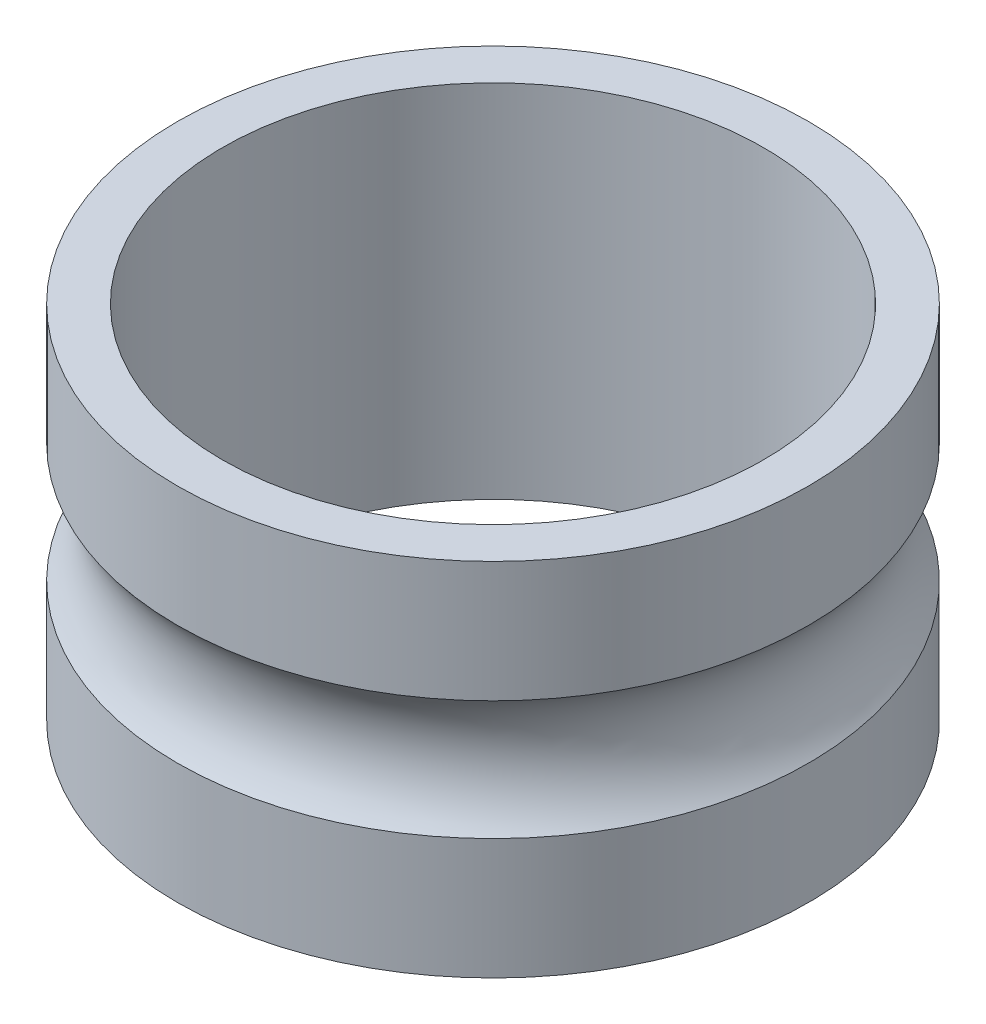
SolidWorks part; units mm, degrees
material "Chrome Stainless Steel"
ref_plane "Front Plane" through (0, 0, 0) normal (0, 0, 1) x (1, 0, 0)
ref_plane "Top Plane" through (0, 0, 0) normal (0, 1, 0) x (1, 0, 0)
ref_plane "Right Plane" through (0, 0, 0) normal (1, 0, 0) x (0, 0, -1)
sketch "DiaProfileS" plane through (0, 0, 0) normal (0, 1, 0) x (1, 0, 0)
  circle A0 centre (0, 0) radius 1.5
  circle A1 centre (0, 0) radius 1.75
  dimension "InnerDia" = 3
  dimension "Thickness" = 0.25
extrude "DiaProfile" add sketch "DiaProfileS" along normal mid plane 2
sketch "BearingPathProfileS" plane through (0, 0, 0) normal (0, 0, 1) x (1, 0, 0)
  line L0 (0, 0) -> (2.125, 0) construction
  line L3 (0, 1) -> (0, -1) construction
  circle A0 centre (2.125, 0) radius 0.5
  dimension "BallDia" = 1
  dimension "YDim" = 0.375
  dimension "RefRadius" = 2.125
revolve "BearingPathProfile" cut sketch "BearingPathProfileS" angle 360 about axis through (0, 1, 0) along (0, -1, 0)
